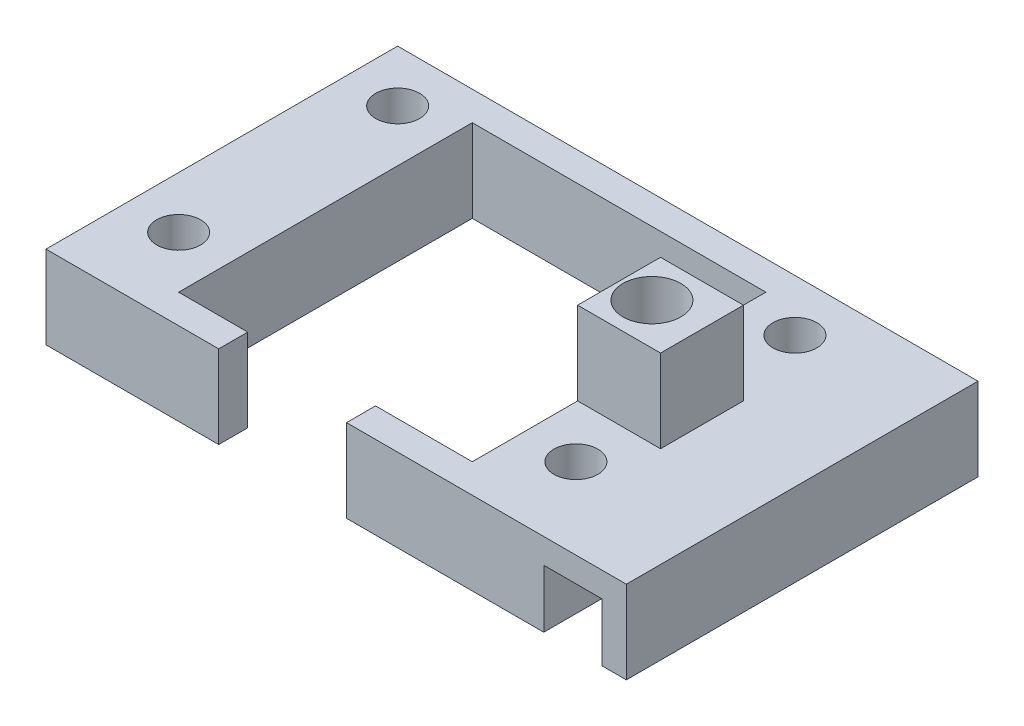
SolidWorks part; units mm, degrees
ref_plane "Front Plane" through (0, 0, 0) normal (0, 0, 1) x (1, 0, 0)
ref_plane "Top Plane" through (0, 0, 0) normal (0, 1, 0) x (1, 0, 0)
ref_plane "Right Plane" through (0, 0, 0) normal (1, 0, 0) x (0, 0, -1)
sketch "Sketch1" plane through (0, 0, 0) normal (0, 1, 0) x (1, 0, 0)
  line L1 (0, 0) -> (42.5, 0)
  line L2 (0, 0) -> (0, 42.5)
  line L3 (0, 42.5) -> (42.5, 42.5)
  line L4 (42.5, 0) -> (42.5, 42.5)
  line L5 (-15, 0) -> (53.5, 0)
  line L6 (-15, 0) -> (-15, 46.7)
  line L7 (-15, 46.7) -> (53.5, 46.7)
  line L8 (53.5, 0) -> (53.5, 46.7)
  line L9 (-15, 0) -> (10, 0)
  line L10 (-15, 0) -> (-15, -4.2)
  line L11 (-15, -4.2) -> (10, -4.2)
  line L12 (10, 0) -> (10, -4.2)
  line L13 (53.5, 0) -> (28.5, 0)
  line L14 (53.5, 0) -> (53.5, -4.2)
  line L15 (53.5, -4.2) -> (28.5, -4.2)
  line L16 (28.5, 0) -> (28.5, -4.2)
  circle A0 centre (-7.5, 7.5) radius 3.175
  circle A2 centre (50, 39.2) radius 3.175
  circle A3 centre (50, 7.5) radius 3.175
  circle A4 centre (-7.5, 39.2) radius 3.175
  point P20 (0, 0)
  point P21 (0, 0)
  point P25 (0, 0)
  point P26 (0, 0)
  dimension "D5" = 7.5
  dimension "D7" = 6.35
  dimension "D1" = 42.5
  dimension "D2" = 11
  dimension "D3" = 15
  dimension "D4" = 4.2
  dimension "D6" = 7.5
  dimension "D8" = 7.5
  dimension "D9" = 3.5
  dimension "D10" = 4.2
  dimension "D11" = 10
extrude "Boss-Extrude1" add sketch "Sketch1" along normal blind 12
sketch "Sketch4" plane through (53.3, 0, 4.2) normal (0, 0, -1) x (-1, 0, 0)
  line L0 (-3.75, 8.4) -> (-0.2, 8.4) construction
  line L1 (-15.7, 0) -> (-0.2, 0)
  line L2 (-15.7, 0) -> (-15.7, 12)
  line L3 (-15.7, 12) -> (-0.2, 12)
  line L4 (-0.2, 0) -> (-0.2, 12)
  line L5 (-12.15, 0) -> (-3.75, 0)
  line L6 (-12.15, 0) -> (-12.15, 8.4)
  line L7 (-12.15, 8.4) -> (-3.75, 8.4)
  line L8 (-3.75, 0) -> (-3.75, 8.4)
  line L9 (-12.15, 8.4) -> (-15.7, 8.4) construction
  line M16 (-0.2, 0) -> (-0.2, 12)
  dimension "D1" = 15.5
  dimension "D2" = 12
  dimension "D3" = 8.4
extrude "Boss-Extrude2" add sketch "Sketch4" along normal up to surface (50.9 mm away) contours L1 L8 L7 L6 L2 L3 L4 M16 up to face at (19.25, 6, -46.7)
sketch "Sketch5" plane through (0, 12, 0) normal (0, 1, 0) x (1, 0, 0)
  line L0 (42.5, 0) -> (42.5, 42.5) construction
  line L1 (42.5, 27.25) -> (54.5, 27.25)
  line L2 (42.5, 27.25) -> (42.5, 15.25)
  line L3 (42.5, 15.25) -> (54.5, 15.25)
  line L4 (54.5, 27.25) -> (54.5, 15.25)
  line L5 (21.25, 42.5) -> (21.25, -4.8094) construction
  line L7 (0, 42.5) -> (42.5, 42.5) construction
  line L8 (54.5, 21.25) -> (42.5, 21.25) construction
  circle A0 centre (47.25, 21.25) radius 4.2
  point P11 (21.25, 42.5)
  point P17 (42.5, 21.25)
  dimension "D2" = 8.4
  dimension "D1" = 26
  dimension "D3" = 12
  dimension "D4" = 12
extrude "Boss-Extrude3" add sketch "Sketch5" along normal blind 12
equation "\"8mm hole\"= 8.4mm"
equation "\"22mm hole\"= 23mm"
equation "\"15mm hole\"= 15.8mm"
equation "\"bed height offset\"= 3mm"
equation "\"motor width\"= 42.5mm"
equation "\"D3@Sketch4\"= \"8mm hole\""
equation "\"D2@Sketch5\"= \"8mm hole\""
